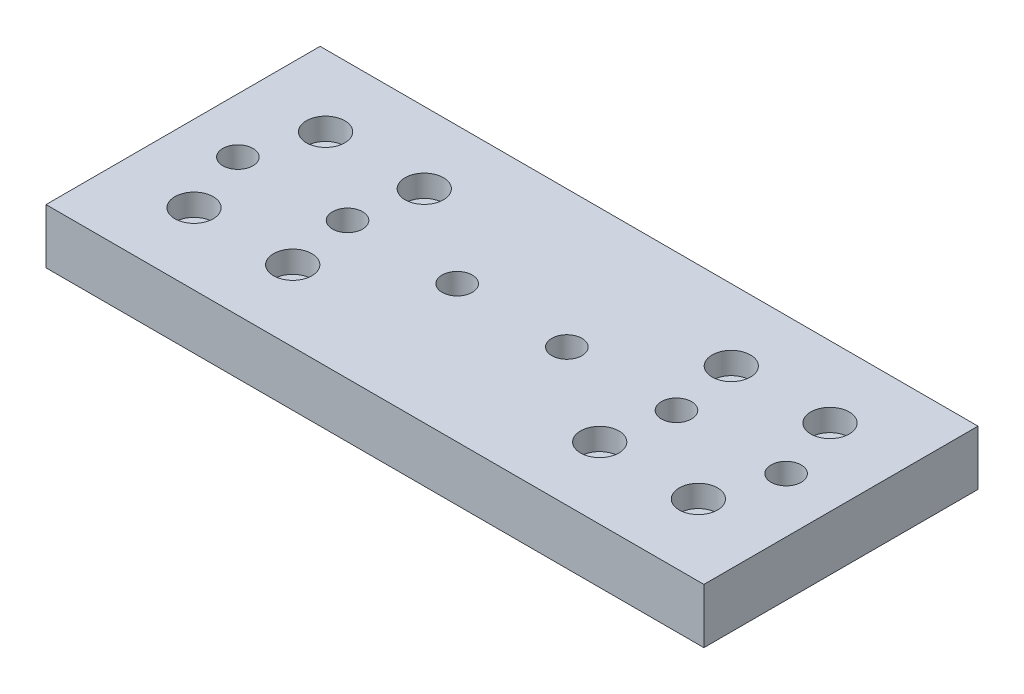
SolidWorks part; units mm, degrees
ref_plane "Front Plane" through (0, 0, 0) normal (0, 0, 1) x (1, 0, 0)
ref_plane "Top Plane" through (0, 0, 0) normal (0, 1, 0) x (1, 0, 0)
ref_plane "Right Plane" through (0, 0, 0) normal (1, 0, 0) x (0, 0, -1)
sketch "Sketch1" plane through (0, 0, 0) normal (0, 1, 0) x (1, 0, 0)
  line L1 (60, -25) -> (-60, -25)
  line L2 (60, -25) -> (60, 25)
  line L3 (60, 25) -> (-60, 25)
  line L4 (-60, -25) -> (-60, 25)
  line L5 (60, -25) -> (-60, 25) construction
  line L6 (60, 25) -> (-60, -25) construction
  point P0 (0, 0)
  dimension "D1" = 50
  dimension "D2" = 120
extrude "main" add sketch "Sketch1" along normal blind 10
sketch "Sketch2" plane through (0, 10, 0) normal (0, 1, 0) x (1, 0, 0)
  line L0 (-60, 0) -> (0, 0) construction
  line L1 (-60, 25) -> (-60, -25) construction
  line L2 (0, 0) -> (0, 25) construction
  line L3 (60, 25) -> (-60, 25) construction
  circle A0 centre (-28, -12) radius 1.5
  circle A1 centre (-46, -12) radius 1.5
  circle A3 centre (28, -12) radius 1.5
  circle A5 centre (46, -12) radius 1.5
  circle A7 centre (46, 12) radius 1.5
  circle A9 centre (28, 12) radius 1.5
  circle A12 centre (-46, 12) radius 1.5
  circle A16 centre (-28, 12) radius 1.5
  dimension "D1" = 3
  dimension "D2" = 24
  dimension "D3" = 18
  dimension "D4" = 14
extrude "linear_bearing_mount" cut sketch "Sketch2" against normal through all
sketch "Sketch5" plane through (0, 10, 0) normal (0, 1, 0) x (1, 0, 0)
  line L0 (0, 25) -> (0, 0) construction
  line L1 (60, 25) -> (-60, 25) construction
  line L2 (0, 0) -> (-60, 0) construction
  line L3 (-60, 25) -> (-60, -25) construction
  circle A0 centre (-46, 12) radius 3.5
  circle A1 centre (-28, 12) radius 3.5
  circle A2 centre (-28, -12) radius 3.5
  circle A3 centre (-46, -12) radius 3.5
  circle A4 centre (46, -12) radius 3.5
  circle A5 centre (28, -12) radius 3.5
  circle A6 centre (28, 12) radius 3.5
  circle A7 centre (46, 12) radius 3.5
  dimension "D1" = 7
extrude "linear_bearing_countersink" cut sketch "Sketch5" against normal blind 4
sketch "Sketch6" plane through (0, 0, 0) normal (0, -1, 0) x (1, 0, 0)
  line L0 (-60, 0) -> (60, 0) construction
  line L3 (-60, -25) -> (-60, 25) construction
  line L4 (60, 25) -> (60, -25) construction
  line L5 (-50, 0) -> (-30, 0) construction
  line L6 (0, 25) -> (0, -25) construction
  line L7 (-60, 25) -> (60, 25) construction
  line L8 (60, -25) -> (-60, -25) construction
  circle A4 centre (-50, 0) radius 2.5
  circle A5 centre (-30, 0) radius 2.5
  circle A6 centre (-10, 0) radius 2.5
  circle A7 centre (10, 0) radius 2.5
  circle A8 centre (30, 0) radius 2.5
  circle A9 centre (50, 0) radius 2.5
  dimension "D3" = 5
  dimension "D1" = 6
  dimension "D2" = 20
extrude "Cut-Extrude1" cut sketch "Sketch6" against normal through all
sketch "Sketch7" plane through (0, 0, 0) normal (0, -1, 0) x (1, 0, 0)
  circle A0 centre (-50, 0) radius 4.3
  circle A1 centre (-30, 0) radius 4.3
  circle A2 centre (-10, 0) radius 4.3
  circle A3 centre (10, 0) radius 4.3
  circle A4 centre (30, 0) radius 4.3
  circle A5 centre (50, 0) radius 4.3
  dimension "D1" = 8.6
extrude "Cut-Extrude2" [suppressed] cut sketch "Sketch7" against normal blind 5
hole_wizard "CSK for M5 socket countersunk head screw1" positions "Sketch8" profile "Sketch9" countersink size "M5" standard "DIN"
sketch "Sketch8" plane through (0, 0, 0) normal (0, -1, 0) x (-1, 0, 0)
  point P0 (-50, 0)
  point P3 (-30, 0)
  point P6 (-10, 0)
  point P9 (10, 0)
  point P12 (30, 0)
  point P15 (50, 0)
sketch "Sketch9" plane through (50, 0, 0) normal (1, 0, 0) x (0, 0, -1)
  line L0 (0, 0) -> (0, 11.6524)
  line L1 (0, 11.6524) -> (2.75, 10)
  line L2 (2.75, 10) -> (2.75, 2.985)
  line L3 (2.75, 2.985) -> (5.735, 0)
  line L5 (5.735, 0) -> (0, 0)
  line L6 (-2.75, 2.985) -> (-5.735, 0) construction
  line L10 (0, 11.6524) -> (-2.75, 10) construction
  line L11 (0, -6.35) -> (0, 107.95) construction
  dimension "Hole Dia." = 5.5
  dimension "Hole Depth" = 10
  dimension "Near C'Sink Dia." = 11.47
  dimension "Near C'Sink Angle" = 90
  dimension "Drill Angle" = 118
